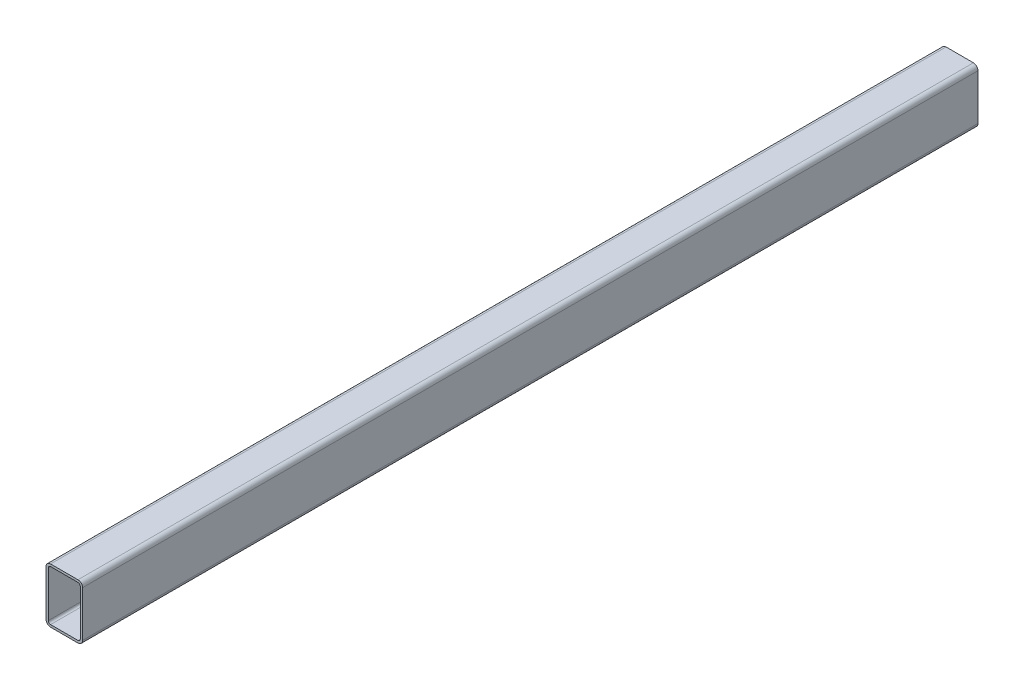
SolidWorks part; units mm, degrees
material "Plain Carbon Steel"
ref_plane "Front Plane" through (0, 0, 0) normal (0, 0, 1) x (1, 0, 0)
ref_plane "Top Plane" through (0, 0, 0) normal (0, 1, 0) x (1, 0, 0)
ref_plane "Right Plane" through (0, 0, 0) normal (1, 0, 0) x (0, 0, -1)
sketch "Sketch13" plane through (0, 0, 0) normal (0, 0, 1) x (1, 0, 0)
  line L4 (19.05, -38.1) -> (-19.05, -38.1)
  line L5 (25.4, 31.75) -> (25.4, -31.75)
  line L6 (-25.4, -31.75) -> (-25.4, 31.75)
  line L7 (-19.05, 38.1) -> (19.05, 38.1)
  line L8 (19.05, -34.925) -> (-19.05, -34.925)
  line L9 (22.225, 31.75) -> (22.225, -31.75)
  line L10 (-19.05, 34.925) -> (19.05, 34.925)
  line L11 (-22.225, -31.75) -> (-22.225, 31.75)
  line L12 (-19.05, 31.75) -> (19.05, -31.75) construction
  line L13 (19.05, 31.75) -> (-19.05, -31.75) construction
  arc A4 (-25.4, -31.75) -> (-19.05, -38.1) centre (-19.05, -31.75) ccw
  arc A5 (19.05, -38.1) -> (25.4, -31.75) centre (19.05, -31.75) ccw
  arc A6 (25.4, 31.75) -> (19.05, 38.1) centre (19.05, 31.75) ccw
  arc A7 (-19.05, 38.1) -> (-25.4, 31.75) centre (-19.05, 31.75) ccw
  arc A8 (-22.225, -31.75) -> (-19.05, -34.925) centre (-19.05, -31.75) ccw
  arc A9 (19.05, -34.925) -> (22.225, -31.75) centre (19.05, -31.75) ccw
  arc A10 (22.225, 31.75) -> (19.05, 34.925) centre (19.05, 31.75) ccw
  arc A11 (-19.05, 34.925) -> (-22.225, 31.75) centre (-19.05, 31.75) ccw
  dimension "D4" = 6.35
  dimension "D2" = 50.8
  dimension "D3" = 76.2
  dimension "D1" = 3.175
extrude "Boss-Extrude2" add sketch "Sketch13" along normal mid plane 1244.6 separate body
equation "\"M5_tap\"=4.2mm\t\t\t\t\t\t\t' Below you can do mesurements as follows: cm, mm, ft, in, m, "
equation "\"M5_clearence\"=5.5mm"
equation "\"M6_tap\"=5mm"
equation "\"M6_clearence\"=6.6mm"
